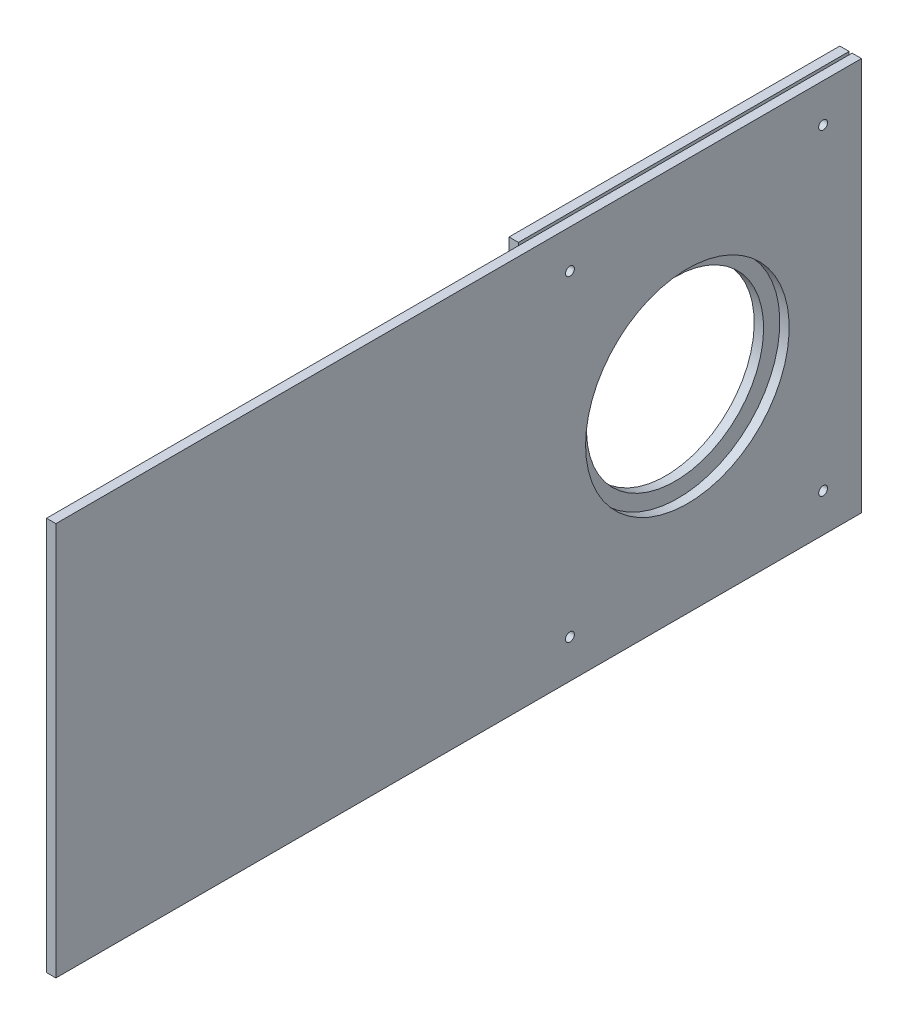
SolidWorks part; units mm, degrees
ref_plane "Front Plane" through (0, 0, 0) normal (0, 0, 1) x (1, 0, 0)
ref_plane "Top Plane" through (0, 0, 0) normal (0, 1, 0) x (1, 0, 0)
ref_plane "Right Plane" through (0, 0, 0) normal (1, 0, 0) x (0, 0, -1)
sketch "Sketch1" plane through (0, 0, 0) normal (0, 0, 1) x (1, 0, 0)
  line L0 (-232.2195, 66.675) -> (232.2195, 66.675) construction
  line L2 (-144.4096, 66.675) -> (-144.4096, -66.675)
  line L3 (-144.4096, -66.675) -> (-141.2346, -66.675)
  line L4 (-141.2346, 66.675) -> (-141.2346, -66.675)
  line L5 (-232.2195, -66.675) -> (232.2195, -66.675) construction
  line L6 (-148.5846, 66.675) -> (-145.4096, 66.675)
  line L7 (-148.5846, 66.675) -> (-148.5846, -66.675)
  line L8 (-148.5846, -66.675) -> (-145.4096, -66.675)
  line L9 (-145.4096, 66.675) -> (-145.4096, -66.675)
  line L10 (-144.4096, 66.675) -> (-141.2346, 66.675)
  dimension "D1" = 3.175
  dimension "D2" = 3.175
  dimension "D3" = 1
  dimension "D4" = 0
extrude "Boss-Extrude1" add sketch "Sketch1" along normal blind 273
sketch "Sketch2" plane through (-144.4096, 0, 0) normal (-1, 0, 0) x (0, 0, 1)
  line L0 (4.0425, 0) -> (-4.0425, 0) construction
  line L1 (0, -4.0425) -> (0, 4.0425) construction
  circle A0 centre (59, 0) radius 34.5
  dimension "D1" = 59
  dimension "D2" = 69
sketch "Sketch3" plane through (-145.4096, 0, 0) normal (1, 0, 0) x (0, 0, -1)
  circle A0 centre (-59, 0) radius 30
  dimension "D1" = 60
extrude "Cut-Extrude2" cut sketch "Sketch3" against normal blind 295 contours A0
extrude "Cut-Extrude3" cut sketch "Sketch2" along normal blind 100 and the other way blind 13 contours A0
sketch "Sketch4" plane through (-148.5846, 0, 0) normal (-1, 0, 0) x (0, 0, 1)
  line L1 (273, 66.675) -> (0, 66.675) construction
  line L2 (273, -66.675) -> (0, -66.675) construction
  line L4 (0, -4.0425) -> (0, 4.0425) construction
  circle A2 centre (13, -53.675) radius 1.5
  circle A3 centre (13, 53.675) radius 1.5
  circle A4 centre (98.797, -53.675) radius 1.5
  circle A5 centre (98.797, 53.675) radius 1.5
  point P0 (98.797, 53.675)
  dimension "D1" = 3
  dimension "D2" = 3
  dimension "D4" = 3
  dimension "D7" = 3
  dimension "D3" = 13
  dimension "D5" = 13
  dimension "D6" = 13
  dimension "D8" = 13
extrude "Cut-Extrude4" cut sketch "Sketch4" against normal blind 63 and the other way blind 3
sketch "Sketch5" plane through (-148.5846, 0, 0) normal (-1, 0, 0) x (0, 0, 1)
  line L1 (112.088, 68.3536) -> (276.7333, 68.3536)
  line L2 (112.088, 68.3536) -> (112.088, -69.1673)
  line L3 (112.088, -69.1673) -> (276.7333, -69.1673)
  line L4 (276.7333, 68.3536) -> (276.7333, -69.1673)
extrude "Cut-Extrude5" cut sketch "Sketch5" along normal blind 11 and the other way blind 4
